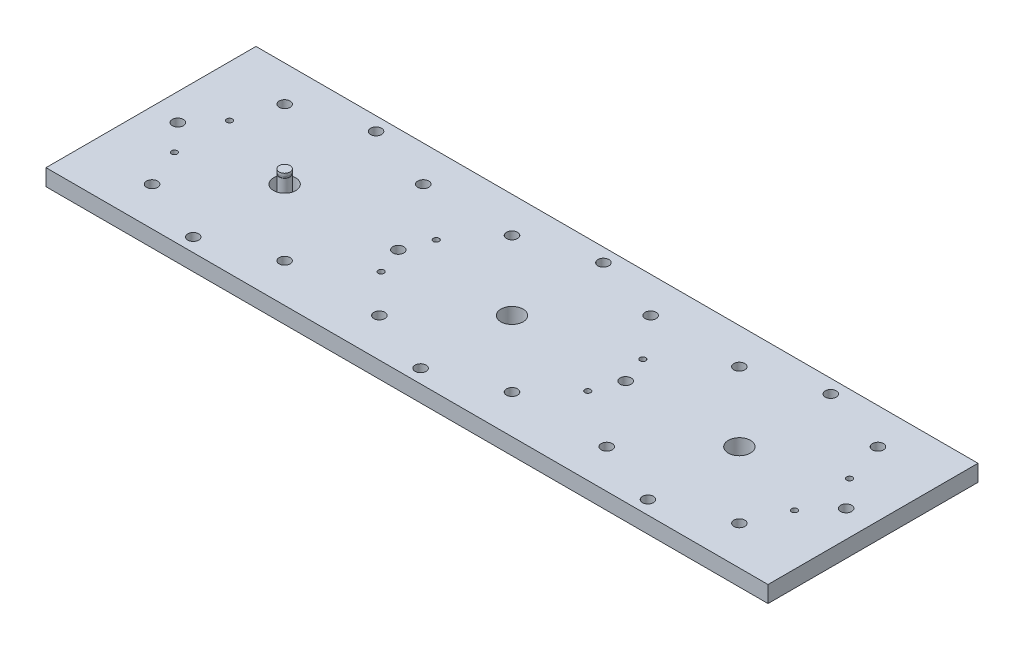
SolidWorks part; units mm, degrees
ref_plane "Front Plane" through (0, 0, 0) normal (0, 0, 1) x (1, 0, 0)
ref_plane "Top Plane" through (0, 0, 0) normal (0, 1, 0) x (1, 0, 0)
ref_plane "Right Plane" through (0, 0, 0) normal (1, 0, 0) x (0, 0, -1)
sketch "Sketch1" plane through (0, 0, 0) normal (0, 1, 0) x (1, 0, 0)
  line L0 (-338.0645, 0) -> (0, 0) construction
  line L1 (0, 0) -> (0, 399.1039) construction
  line L3 (-262, 76.2) -> (262, 76.2)
  line L4 (-262, 76.2) -> (-262, -76.2)
  line L5 (-262, -76.2) -> (262, -76.2)
  line L6 (262, 76.2) -> (262, -76.2)
  circle A0 centre (-165, 0) radius 8.05
  circle A1 centre (0, 0) radius 8.05
  circle A2 centre (165, 0) radius 8.05
  dimension "D3" = 330
  dimension "D4" = 16.1
  dimension "D1" = 524
  dimension "D2" = 152.4
extrude "Boss-Extrude1" add sketch "Sketch1" along normal mid plane 12
hole_wizard "M5 Tapped Hole1" positions "Sketch2" profile "Sketch4" tap size "M5" standard "ISO" end condition through all
sketch "Sketch2" plane through (0, 6, 0) normal (0, 1, 0) x (1, 0, 0)
  line L2 (0, 0) -> (0, 102.7539) construction
  line L5 (0, 0) -> (-206.9382, 0) construction
  point P0 (-75, 20)
  point P19 (-225, 20)
  point P23 (-225, -20)
  point P24 (-75, -20)
  point P26 (225, 20)
  point P27 (225, -20)
  point P28 (75, -20)
  point P29 (75, 20)
  dimension "D1" = 40
  dimension "D2" = 150
  dimension "D3" = 150
sketch "Sketch4" plane through (-75, 6, -20) normal (1, 0, 0) x (0, 0, 1)
  line L0 (0, 0) -> (0, 12)
  line L1 (0, 12) -> (2.1, 12)
  line L2 (2.1, 12) -> (2.1, 0)
  line L5 (2.1, 0) -> (0, 0)
  line L11 (0, -6.35) -> (0, 107.95) construction
  dimension "Thru Tap Drill Dia." = 4.2
  dimension "Thru Tap Drill Depth" = 12
cosmetic thread "Hole Thread1" parameters "D2"=5
cosmetic thread "Hole Thread2" parameters "D2"=5
cosmetic thread "Hole Thread3" parameters "D2"=5
cosmetic thread "Hole Thread4" parameters "D2"=5
cosmetic thread "Hole Thread5" parameters "D2"=5
cosmetic thread "Hole Thread6" parameters "D2"=5
cosmetic thread "Hole Thread7" parameters "D2"=5
cosmetic thread "Hole Thread8" parameters "D2"=5
hole_wizard "CBORE for M4 Hex Socket Head Cap Screw1" positions "Sketch8" profile "Sketch9" counterbore size "M4" standard "ISO" end condition through all
sketch "Sketch8" plane through (0, 6, 0) normal (0, 1, 0) x (1, 0, 0)
  point P15 (-242.5, 0)
  point P17 (-215.2973, 50.2973)
  point P19 (-213.1185, -48.1185)
  point P21 (-165, -66.3379)
  point P23 (-165, 66.3381)
  point P25 (-114.7027, 50.2973)
  point P27 (-116.8815, -48.1185)
  point P29 (-82.5, 0)
  point P31 (-48.1185, -48.1185)
  point P33 (-50.2973, 50.2973)
  point P36 (0, 66.3381)
  point P38 (0, -66.3379)
  point P40 (48.1185, -48.1185)
  point P42 (50.2973, 50.2973)
  point P44 (82.5, 0)
  point P46 (114.7027, 50.2973)
  point P48 (116.8815, -48.1185)
  point P50 (165, -66.3379)
  point P52 (165, 66.3381)
  point P54 (215.2973, 50.2973)
  point P56 (213.1185, -48.1185)
  point P58 (242.5, 0)
sketch_block_instance "StandoffPattern2-1"
sketch_block "StandoffPattern2"
sketch "Sketch9" plane through (-242.5, 6, 0) normal (1, 0, 0) x (0, 0, 1)
  line L0 (0, 0) -> (0, 12)
  line L1 (0, 12) -> (2.25, 12)
  line L3 (2.25, 12) -> (2.25, 9.4)
  line L4 (2.25, 9.4) -> (4, 9.4)
  line L5 (4, 9.4) -> (4, 0)
  line L7 (4, 0) -> (0, 0)
  line L11 (0, -6.35) -> (0, 107.95) construction
  dimension "Thru Hole Dia." = 4.5
  dimension "Thru Hole Depth" = 12
  dimension "C'Bore Dia." = 8
  dimension "C'Bore Depth" = 9.4
sketch "Sketch10" plane through (0, 0, 0) normal (0, 0, 1) x (1, 0, 0)
  line L0 (-165, 25.8323) -> (-165, -60) construction
  line L1 (-173.05, 6) -> (-173.05, -6) construction
  line L2 (-156.95, -6) -> (-156.95, 6) construction
  line L3 (-165, -60) -> (-176, -60)
  line L4 (-176, -60) -> (-176, -57)
  line L5 (-176, -57) -> (-169, -57)
  line L6 (-169, -57) -> (-169, 12.5)
  line L7 (-169, 12.5) -> (-168.75, 12.5)
  line L8 (-168.75, 12.5) -> (-168.75, 13.7)
  line L9 (-168.75, 13.7) -> (-169, 13.7)
  line L10 (-169, 13.7) -> (-169, 15.7)
  line L11 (-169, 15.7) -> (-165, 15.7)
  line L13 (-165, -60) -> (-165, 15.7)
  line L14 (-262, -6) -> (262, -6) construction
  line L15 (-173.05, 0) -> (-180.6927, 0) construction
  line L18 (-173, 12.5) -> (-169, 12.5) construction
  line L19 (-173, 12.5) -> (-173, -12.5) construction
  line L20 (-173, -12.5) -> (-169, -12.5) construction
  line L21 (-169, 12.5) -> (-169, -12.5) construction
  dimension "D1" = 8
  dimension "D2" = 22
  dimension "D3" = 3
  dimension "D4" = 25
  dimension "D5" = 7.5
  dimension "D6" = 1.2
  dimension "D7" = 2
  dimension "D8" = 54
  dimension "D9" = 8
  dimension "D10" = 12.5
revolve "Revolve1" add sketch "Sketch10" angle 360 about L0
